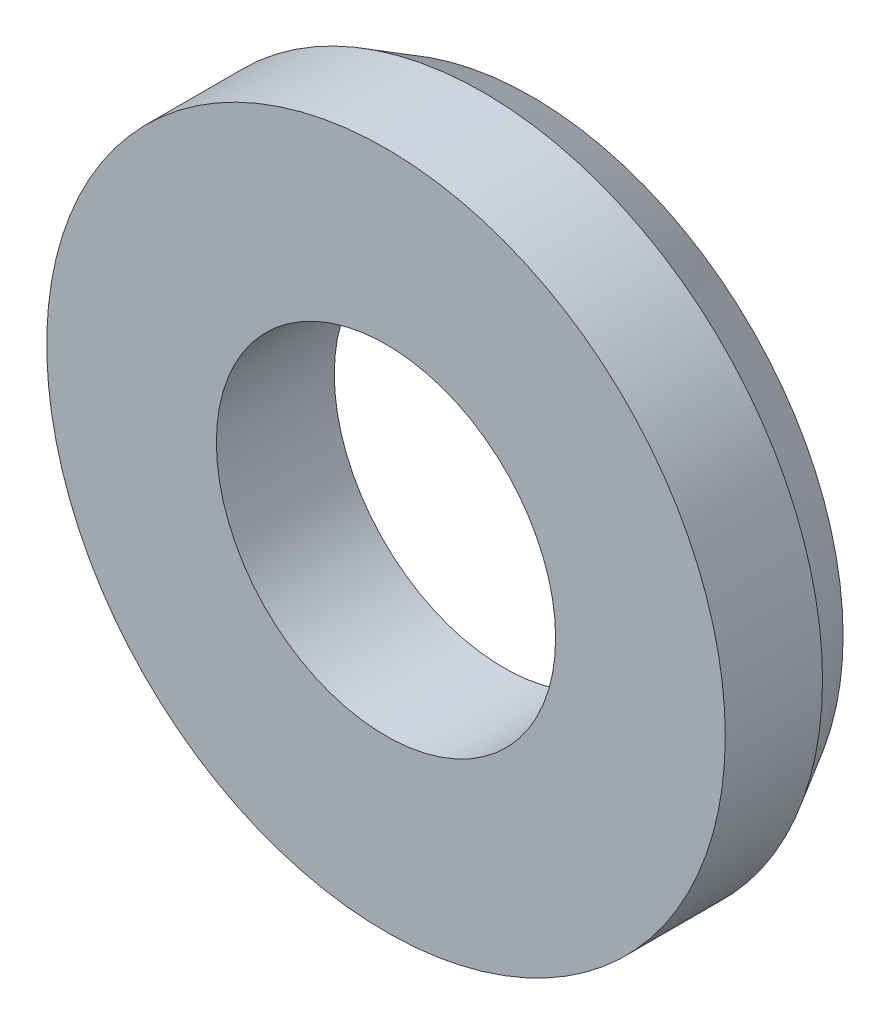
SolidWorks part; units mm, degrees
ref_plane "Alzado" through (0, 0, 0) normal (0, 0, 1) x (1, 0, 0)
ref_plane "Planta" through (0, 0, 0) normal (0, 1, 0) x (1, 0, 0)
ref_plane "Vista lateral" through (0, 0, 0) normal (1, 0, 0) x (0, 0, -1)
sketch "Sketch1" plane through (0, 0, 0) normal (0, 1, 0) x (1, 0, 0)
  line L0 (0.9172, 1.15) -> (0.75, 1.15)
  line L1 (0.5, 1.0676) -> (0.5, 0.72)
  line L2 (0.5, 0.72) -> (1, 0.72)
  line L3 (1, 0.72) -> (1, 1.0067)
  line L4 (1, 1.0067) -> (0.9172, 1.15)
  line L5 (0, 1.15) -> (0, 0.72) construction
  arc A0 (0.75, 1.15) -> (0.5, 1.0676) centre (0, 3.004) cw
  dimension "D1" = 2
  dimension "D2" = 0.5
  dimension "D3" = 0.75
  dimension "D4" = 0.9172
  dimension "D5" = 1
  dimension "D6" = 0.2867
  dimension "D7" = 0.3476
revolve "Revolve1" add sketch "Sketch1" angle 360 about L5
